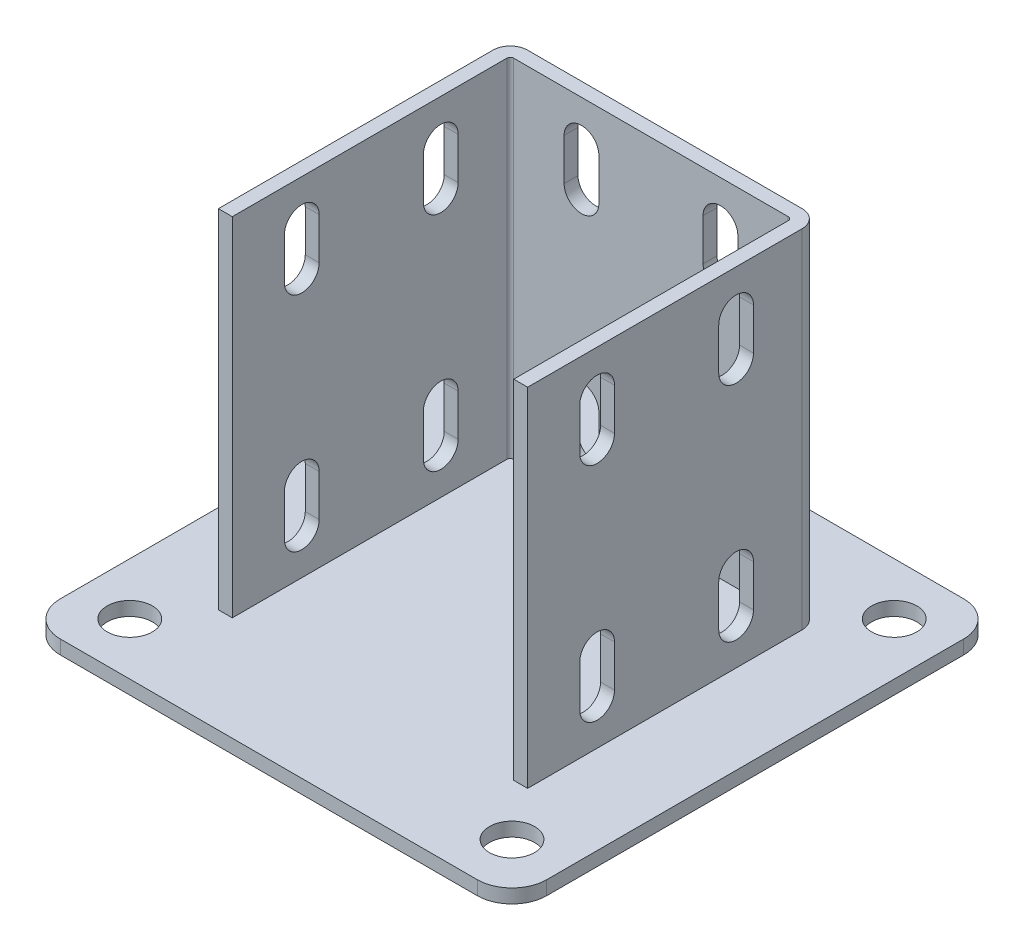
SolidWorks part; units mm, degrees
material "Ст3пс ГОСТ 380-2005"
ref_plane "Спереди" through (0, 0, 0) normal (0, 0, 1) x (1, 0, 0)
ref_plane "Сверху" through (0, 0, 0) normal (0, 1, 0) x (1, 0, 0)
ref_plane "Справа" through (0, 0, 0) normal (1, 0, 0) x (0, 0, -1)
sketch "Эскиз2" plane through (0, 0, 0) normal (0, 1, 0) x (1, 0, 0)
  line L1 (-70, -70) -> (70, -70)
  line L2 (-70, -70) -> (-70, 70)
  line L3 (-70, 70) -> (70, 70)
  line L4 (70, -70) -> (70, 70)
  line L5 (-70, -70) -> (70, 70) construction
  line L6 (-70, 70) -> (70, -70) construction
  point P0 (0, 0)
  dimension "D2" = 140
extrude "Бобышка-Вытянуть1" add sketch "Эскиз2" along normal blind 4
sketch "Эскиз3" plane through (0, 4, 0) normal (0, 1, 0) x (1, 0, 0)
  line L0 (-40.5, -40) -> (-40.5, 40)
  line L1 (-40.5, 40) -> (40.5, 40)
  line L2 (40.5, 40) -> (40.5, -40)
  point P2 (0, 40)
  point P5 (-40.5, 0)
  dimension "D2" = 81
  dimension "D3" = 80
extrude "Вытянуть-Тонкостенный1" add sketch "Эскиз3" along normal offset from surface (100 mm away) 104 thin up to face at (0, 0, 0) thin type one direction reverse wall 4
sketch "Эскиз4" plane through (0, 0, 0) normal (1, 0, 0) x (0, 0, -1)
  line L0 (44, 40.3731) -> (65, 4)
  line L1 (44, 104) -> (44, 4) construction
  line L2 (-70, 4) -> (70, 4) construction
  line L3 (65, 4) -> (44, 4)
  line L4 (44, 4) -> (44, 40.3731)
  line L5 (70, 4) -> (70, 0) construction
  dimension "D1" = 30
  dimension "D2" = 5
extrude "Бобышка-Вытянуть2" add sketch "Эскиз4" along normal mid plane 4
sketch "Эскиз5" plane through (44.5, 0, 0) normal (1, 0, 0) x (0, 0, -1)
  line L0 (-20, 92) -> (-20, 80) construction
  line L1 (-15, 92) -> (-15, 80)
  line L2 (-25, 92) -> (-25, 80)
  line L3 (-20, 28) -> (-20, 16) construction
  line L4 (-15, 28) -> (-15, 16)
  line L5 (-25, 28) -> (-25, 16)
  line L6 (-40, 104) -> (39, 104) construction
  line L7 (-70, 4) -> (70, 4) construction
  line L8 (0, 0) -> (0, 63.8564) construction
  line L11 (20, 92) -> (20, 80) construction
  line L14 (15, 92) -> (15, 80)
  line L15 (25, 92) -> (25, 80)
  line L16 (20, 28) -> (20, 16) construction
  line L17 (15, 28) -> (15, 16)
  line L18 (25, 28) -> (25, 16)
  arc A0 (-15, 92) -> (-25, 92) centre (-20, 92) ccw
  arc A1 (-25, 80) -> (-15, 80) centre (-20, 80) ccw
  arc A2 (-15, 28) -> (-25, 28) centre (-20, 28) ccw
  arc A3 (-25, 16) -> (-15, 16) centre (-20, 16) ccw
  arc A8 (15, 92) -> (25, 92) centre (20, 92) cw
  arc A9 (25, 80) -> (15, 80) centre (20, 80) cw
  arc A10 (15, 28) -> (25, 28) centre (20, 28) cw
  arc A11 (25, 16) -> (15, 16) centre (20, 16) cw
  point P3 (-20, 86)
  point P8 (-20, 22)
  point P22 (20, 86)
  point P29 (20, 22)
extrude "Вырез-Вытянуть1" cut sketch "Эскиз5" against normal through all
sketch "Эскиз6" plane through (0, 4, 0) normal (0, 1, 0) x (1, 0, 0)
  line L0 (-70, 70) -> (-70, -70) construction
  line L1 (55, -55) -> (-55, -55) construction
  line L2 (55, -55) -> (55, 55) construction
  line L3 (55, 55) -> (-55, 55) construction
  line L4 (-55, -55) -> (-55, 55) construction
  line L5 (55, -55) -> (-55, 55) construction
  line L6 (55, 55) -> (-55, -55) construction
  line L7 (70, 70) -> (-70, 70) construction
  circle A0 centre (-55, 55) radius 6.5
  circle A1 centre (-55, -55) radius 6.5
  circle A2 centre (55, 55) radius 6.5
  circle A3 centre (55, -55) radius 6.5
  point P0 (0, 0)
  dimension "D1" = 13
  dimension "D2" = 15
  dimension "D3" = 15
extrude "Вырез-Вытянуть2" cut sketch "Эскиз6" against normal through all
fillet "Скругление1" radius 10 4 edges at (70, 2, 70) (-70, 2, 70) (-70, 2, -70) (70, 2, -70)
sketch "Эскиз8" plane through (0, 0, -44) normal (0, 0, -1) x (-1, 0, 0)
  line L0 (-20, 92) -> (-20, 80) construction
  line L1 (-15, 92) -> (-15, 80)
  line L2 (-25, 92) -> (-25, 80)
  line L3 (-20, 28) -> (-20, 16) construction
  line L4 (-15, 28) -> (-15, 16)
  line L5 (-25, 28) -> (-25, 16)
  line L6 (-39.5, 104) -> (39.5, 104) construction
  line L7 (-60, 4) -> (60, 4) construction
  line L8 (0, 0) -> (0, 80) construction
  line L9 (-60, 0) -> (60, 0) construction
  line L10 (20, 92) -> (20, 80) construction
  line L11 (15, 92) -> (15, 80)
  line L12 (25, 92) -> (25, 80)
  line L13 (20, 28) -> (20, 16) construction
  line L14 (15, 28) -> (15, 16)
  line L15 (25, 28) -> (25, 16)
  arc A0 (-15, 92) -> (-25, 92) centre (-20, 92) ccw
  arc A1 (-25, 80) -> (-15, 80) centre (-20, 80) ccw
  arc A2 (-15, 28) -> (-25, 28) centre (-20, 28) ccw
  arc A3 (-25, 16) -> (-15, 16) centre (-20, 16) ccw
  arc A4 (15, 92) -> (25, 92) centre (20, 92) cw
  arc A5 (25, 80) -> (15, 80) centre (20, 80) cw
  arc A6 (15, 28) -> (25, 28) centre (20, 28) cw
  arc A7 (25, 16) -> (15, 16) centre (20, 16) cw
  point P2 (-20, 86)
  point P7 (-20, 22)
  point P24 (20, 86)
  point P31 (20, 22)
extrude "Вырез-Вытянуть3" cut sketch "Эскиз8" against normal up to next
equation "\"D5@Эскиз5\"=\"D5@Эскиз8\""
